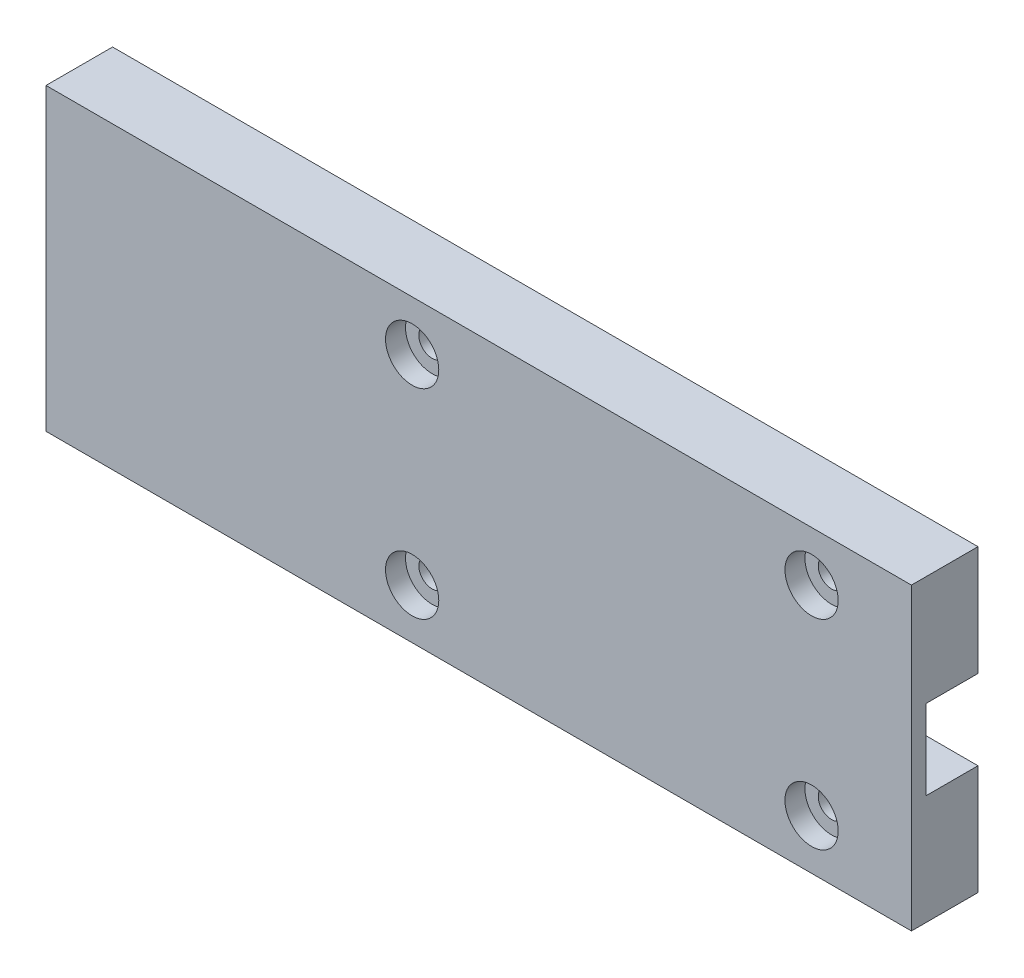
SolidWorks part; units mm, degrees
ref_plane "Front Plane" through (0, 0, 0) normal (0, 0, 1) x (1, 0, 0)
ref_plane "Top Plane" through (0, 0, 0) normal (0, 1, 0) x (1, 0, 0)
ref_plane "Right Plane" through (0, 0, 0) normal (1, 0, 0) x (0, 0, -1)
sketch "Sketch1" plane through (0, 0, 0) normal (0, 0, 1) x (1, 0, 0)
  line L0 (130, 45) -> (130, 0) construction
  line L1 (0, 0) -> (130, 0)
  line L2 (0, 0) -> (0, 45)
  line L3 (0, 45) -> (130, 45)
  line L4 (130, 0) -> (130, 45)
  line L5 (0, 0) -> (130, 45) construction
  line L6 (0, 45) -> (130, 0) construction
  line L7 (0, 45) -> (130, 45) construction
  point P4 (65, 22.5)
extrude "Boss-Extrude1" add sketch "Sketch1" along normal blind 10
sketch "Sketch2" plane through (0, 0, 0) normal (0, 0, -1) x (-1, 0, 0)
  line L0 (-130, 0) -> (-130, 45) construction
  line L1 (-130, 16.5) -> (-20, 16.5)
  line L2 (-130, 16.5) -> (-130, 28.5)
  line L3 (-130, 28.5) -> (-20, 28.5)
  line L4 (-20, 16.5) -> (-20, 28.5)
  line L5 (-130, 16.5) -> (-20, 28.5) construction
  line L6 (-130, 28.5) -> (-20, 16.5) construction
  line L7 (-130, 45) -> (0, 45) construction
  line L8 (0, 0) -> (-130, 0) construction
  point P4 (-75, 22.5)
  dimension "D1" = 16.5
  dimension "D2" = 16.5
  dimension "D3" = 110
extrude "Cut-Extrude1" cut sketch "Sketch2" against normal blind 7.8
sketch "Sketch4" plane through (0, 0, 10) normal (0, 0, 1) x (1, 0, 0)
  line L0 (130, 0) -> (130, 45) construction
  line L1 (115, 7.5) -> (55, 7.5) construction
  line L2 (115, 7.5) -> (115, 37.5) construction
  line L3 (115, 37.5) -> (55, 37.5) construction
  line L4 (55, 7.5) -> (55, 37.5) construction
  line L5 (115, 7.5) -> (55, 37.5) construction
  line L6 (115, 37.5) -> (55, 7.5) construction
  line L7 (130, 22.5) -> (0, 22.5) construction
  line L8 (0, 45) -> (0, 0) construction
  circle A0 centre (55, 37.5) radius 2
  circle A1 centre (115, 37.5) radius 2
  circle A2 centre (115, 7.5) radius 2
  circle A3 centre (55, 7.5) radius 2
  point P0 (85, 22.5)
  dimension "D4" = 4
  dimension "D1" = 30
  dimension "D2" = 60
  dimension "D3" = 15
extrude "Cut-Extrude3" cut sketch "Sketch4" against normal through all
sketch "Sketch5" plane through (0, 0, 10) normal (0, 0, 1) x (1, 0, 0)
  circle A0 centre (55, 37.5) radius 4
  circle A1 centre (115, 37.5) radius 4
  circle A2 centre (115, 7.5) radius 4
  circle A3 centre (55, 7.5) radius 4
  dimension "D1" = 8
extrude "Cut-Extrude4" cut sketch "Sketch5" against normal blind 3
sketch "Sketch6" plane through (0, 0, 0) normal (0, 0, -1) x (-1, 0, 0)
  line L1 (-6.5, 43) -> (-47.5, 43)
  line L2 (-6.5, 43) -> (-6.5, 2)
  line L3 (-6.5, 2) -> (-47.5, 2)
  line L4 (-47.5, 43) -> (-47.5, 2)
  line L5 (-6.5, 43) -> (-47.5, 2) construction
  line L6 (-6.5, 2) -> (-47.5, 43) construction
  point P4 (-27, 22.5)
extrude "Cut-Extrude5" cut sketch "Sketch6" against normal up to surface (7.8 mm away) up to face at (75, 22.5, 7.8)
